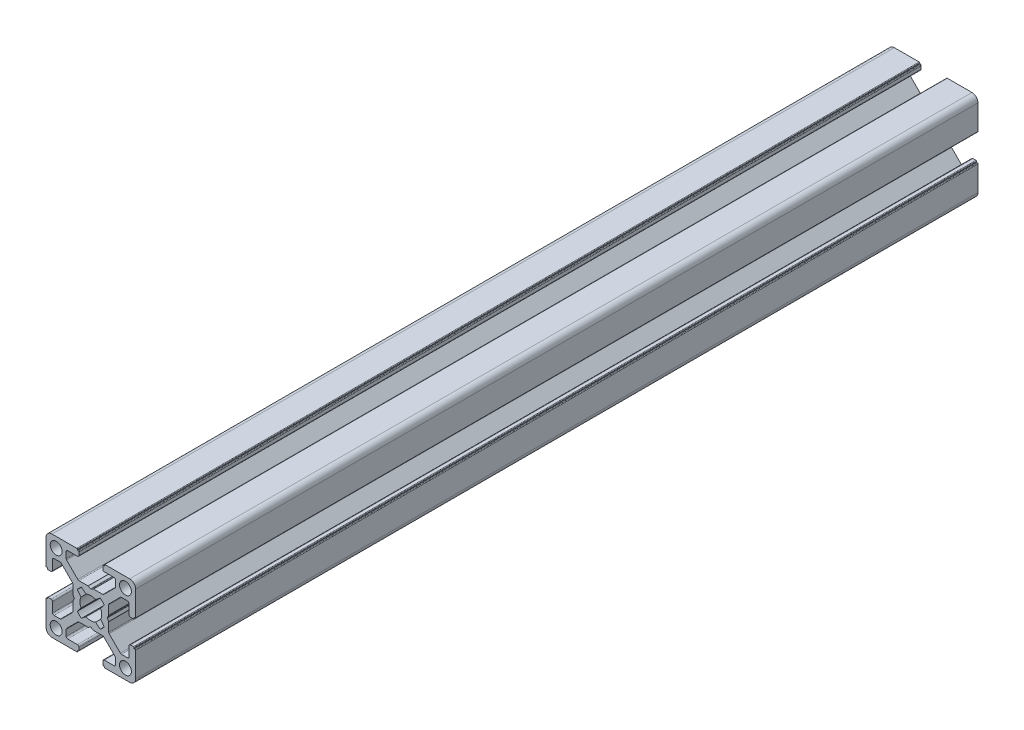
SolidWorks part; units mm, degrees
ref_plane "Alzado" through (0, 0, 0) normal (0, 0, 1) x (1, 0, 0)
ref_plane "Planta" through (0, 0, 0) normal (0, 1, 0) x (1, 0, 0)
ref_plane "Vista lateral" through (0, 0, 0) normal (1, 0, 0) x (0, 0, -1)
ref_plane "Plano1" through (0, 0, 1000) normal (0, 0, 1) x (1, 0, 0)
sketch "Croquis1" plane through (0, 0, 1000) normal (0, 0, 1) x (1, 0, 0)
  line L16 (-7.8359, -10.4816) -> (-6.3001, -11.7194)
  line L17 (-3.0999, -11.7194) -> (-1.5641, -10.4816)
  line L18 (-0.1947, -11.8453) -> (-1.4194, -13.3999)
  line L19 (-1.4194, -16.6001) -> (-0.1947, -18.1547)
  line L20 (-1.5641, -19.5184) -> (-3.0999, -18.2806)
  line L21 (-6.3001, -18.2806) -> (-7.8359, -19.5184)
  line L22 (-9.2053, -18.1547) -> (-7.9806, -16.6001)
  line L23 (-7.9806, -13.3999) -> (-9.2053, -11.8453)
  line L24 (9.8, -10.5) -> (10.1, -10.5)
  line L25 (10.3, -10.3) -> (10.3, -2)
  line L26 (8.3, 0) -> (0, 0)
  line L27 (-0.2, -0.2) -> (-0.2, -0.5)
  line L28 (-0.2, -0.5) -> (-0.5, -0.5)
  line L29 (-0.7, -0.7) -> (-0.7, -1.7)
  line L30 (-0.2, -2.2) -> (3.05, -2.2)
  line L31 (3.55, -2.7) -> (3.55, -4.7431)
  line L32 (3.4037, -5.0964) -> (-0.3491, -8.8534)
  line L33 (-0.7028, -9) -> (-3.7468, -9)
  line L34 (-3.8462, -9.0264) -> (-4.6006, -9.4583)
  line L35 (-4.7994, -9.4583) -> (-5.5538, -9.0264)
  line L36 (-5.6532, -9) -> (-8.6972, -9)
  line L37 (-9.0509, -8.8534) -> (-12.8037, -5.0964)
  line L38 (-12.95, -4.7431) -> (-12.95, -2.7)
  line L39 (-12.45, -2.2) -> (-9.2, -2.2)
  line L40 (-8.7, -1.7) -> (-8.7, -0.7)
  line L41 (-8.9, -0.5) -> (-9.2, -0.5)
  line L42 (-9.2, -0.5) -> (-9.2, -0.2)
  line L43 (-9.4, 0) -> (-17.7, 0)
  line L44 (-19.7, -2) -> (-19.7, -10.3)
  line L45 (-19.5, -10.5) -> (-19.2, -10.5)
  line L46 (-19.2, -10.5) -> (-19.2, -10.8)
  line L47 (-19, -11) -> (-18, -11)
  line L48 (-17.5, -10.5) -> (-17.5, -7.25)
  line L49 (-17, -6.75) -> (-14.9569, -6.75)
  line L50 (-14.6036, -6.8963) -> (-10.8466, -10.6491)
  line L51 (-10.7, -11.0028) -> (-10.7, -14.0468)
  line L52 (-10.6736, -14.1462) -> (-10.2417, -14.9006)
  line L53 (-10.2417, -15.0994) -> (-10.6736, -15.8538)
  line L54 (-10.7, -15.9532) -> (-10.7, -18.9972)
  line L55 (-10.8466, -19.3509) -> (-14.6036, -23.1037)
  line L56 (-14.9569, -23.25) -> (-17, -23.25)
  line L57 (-17.5, -22.75) -> (-17.5, -19.5)
  line L58 (-18, -19) -> (-19, -19)
  line L59 (-19.2, -19.2) -> (-19.2, -19.5)
  line L60 (-19.2, -19.5) -> (-19.5, -19.5)
  line L61 (-19.7, -19.7) -> (-19.7, -28)
  line L62 (-17.7, -30) -> (-9.4, -30)
  line L63 (-9.2, -29.8) -> (-9.2, -29.5)
  line L64 (-9.2, -29.5) -> (-8.9, -29.5)
  line L65 (-8.7, -29.3) -> (-8.7, -28.3)
  line L66 (-9.2, -27.8) -> (-12.45, -27.8)
  line L67 (-12.95, -27.3) -> (-12.95, -25.2569)
  line L68 (-12.8037, -24.9036) -> (-9.0509, -21.1466)
  line L69 (-8.6972, -21) -> (-5.6532, -21)
  line L70 (-5.5538, -20.9736) -> (-4.7994, -20.5417)
  line L71 (-4.6006, -20.5417) -> (-3.8462, -20.9736)
  line L72 (-3.7468, -21) -> (-0.7028, -21)
  line L73 (-0.3491, -21.1466) -> (3.4037, -24.9036)
  line L74 (3.55, -25.2569) -> (3.55, -27.3)
  line L75 (3.05, -27.8) -> (-0.2, -27.8)
  line L76 (-0.7, -28.3) -> (-0.7, -29.3)
  line L77 (-0.5, -29.5) -> (-0.2, -29.5)
  line L78 (-0.2, -29.5) -> (-0.2, -29.8)
  line L79 (0, -30) -> (8.3, -30)
  line L80 (10.3, -28) -> (10.3, -19.7)
  line L81 (10.1, -19.5) -> (9.8, -19.5)
  line L82 (9.8, -19.5) -> (9.8, -19.2)
  line L83 (9.6, -19) -> (8.6, -19)
  line L84 (8.1, -19.5) -> (8.1, -22.75)
  line L85 (7.6, -23.25) -> (5.5569, -23.25)
  line L86 (5.2036, -23.1037) -> (1.4466, -19.3509)
  line L87 (1.3, -18.9972) -> (1.3, -15.9532)
  line L88 (1.2736, -15.8538) -> (0.8417, -15.0994)
  line L89 (0.8417, -14.9006) -> (1.2736, -14.1462)
  line L90 (1.3, -14.0468) -> (1.3, -11.0028)
  line L91 (1.4466, -10.6491) -> (5.2036, -6.8963)
  line L92 (5.5569, -6.75) -> (7.6, -6.75)
  line L93 (8.1, -7.25) -> (8.1, -10.5)
  line L94 (8.6, -11) -> (9.6, -11)
  line L95 (9.8, -10.8) -> (9.8, -10.5)
  line L96 (8, -2.3) -> (5.8, -4.5) construction
  line L97 (-15.2, -2.3) -> (-17.4, -4.5) construction
  line L98 (-4.7, -15) -> (6.9, -15) construction
  arc A16 (-9.2053, -11.8453) -> (-7.8359, -10.4816) centre (-4.7, -15) cw
  arc A17 (-6.3001, -11.7194) -> (-3.0999, -11.7194) centre (-4.7, -15) cw
  arc A18 (-1.5641, -10.4816) -> (-0.1947, -11.8453) centre (-4.7, -15) cw
  arc A19 (-1.4194, -13.3999) -> (-1.4194, -16.6001) centre (-4.7, -15) cw
  arc A20 (-0.1947, -18.1547) -> (-1.5641, -19.5184) centre (-4.7, -15) cw
  arc A21 (-3.0999, -18.2806) -> (-6.3001, -18.2806) centre (-4.7, -15) cw
  arc A22 (-7.8359, -19.5184) -> (-9.2053, -18.1547) centre (-4.7, -15) cw
  arc A23 (-7.9806, -16.6001) -> (-7.9806, -13.3999) centre (-4.7, -15) cw
  arc A24 (10.1, -10.5) -> (10.3, -10.3) centre (10.1, -10.3) ccw
  arc A25 (10.3, -2) -> (8.3, 0) centre (8.3, -2) ccw
  arc A26 (0, 0) -> (-0.2, -0.2) centre (0, -0.2) ccw
  arc A27 (-0.5, -0.5) -> (-0.7, -0.7) centre (-0.5, -0.7) ccw
  arc A28 (-0.7, -1.7) -> (-0.2, -2.2) centre (-0.2, -1.7) ccw
  arc A29 (3.05, -2.2) -> (3.55, -2.7) centre (3.05, -2.7) cw
  arc A30 (3.55, -4.7431) -> (3.4037, -5.0964) centre (3.05, -4.7431) cw
  arc A31 (-0.3491, -8.8534) -> (-0.7028, -9) centre (-0.7028, -8.5) cw
  arc A32 (-3.7468, -9) -> (-3.8462, -9.0264) centre (-3.7468, -9.2) ccw
  arc A33 (-4.6006, -9.4583) -> (-4.7994, -9.4583) centre (-4.7, -9.2847) cw
  arc A34 (-5.5538, -9.0264) -> (-5.6532, -9) centre (-5.6532, -9.2) ccw
  arc A35 (-8.6972, -9) -> (-9.0509, -8.8534) centre (-8.6972, -8.5) cw
  arc A36 (-12.8037, -5.0964) -> (-12.95, -4.7431) centre (-12.45, -4.7431) cw
  arc A37 (-12.95, -2.7) -> (-12.45, -2.2) centre (-12.45, -2.7) cw
  arc A38 (-9.2, -2.2) -> (-8.7, -1.7) centre (-9.2, -1.7) ccw
  arc A39 (-8.7, -0.7) -> (-8.9, -0.5) centre (-8.9, -0.7) ccw
  arc A40 (-9.2, -0.2) -> (-9.4, 0) centre (-9.4, -0.2) ccw
  arc A41 (-17.7, 0) -> (-19.7, -2) centre (-17.7, -2) ccw
  arc A42 (-19.7, -10.3) -> (-19.5, -10.5) centre (-19.5, -10.3) ccw
  arc A43 (-19.2, -10.8) -> (-19, -11) centre (-19, -10.8) ccw
  arc A44 (-18, -11) -> (-17.5, -10.5) centre (-18, -10.5) ccw
  arc A45 (-17.5, -7.25) -> (-17, -6.75) centre (-17, -7.25) cw
  arc A46 (-14.9569, -6.75) -> (-14.6036, -6.8963) centre (-14.9569, -7.25) cw
  arc A47 (-10.8466, -10.6491) -> (-10.7, -11.0028) centre (-11.2, -11.0028) cw
  arc A48 (-10.7, -14.0468) -> (-10.6736, -14.1462) centre (-10.5, -14.0468) ccw
  arc A49 (-10.2417, -14.9006) -> (-10.2417, -15.0994) centre (-10.4153, -15) cw
  arc A50 (-10.6736, -15.8538) -> (-10.7, -15.9532) centre (-10.5, -15.9532) ccw
  arc A51 (-10.7, -18.9972) -> (-10.8466, -19.3509) centre (-11.2, -18.9972) cw
  arc A52 (-14.6036, -23.1037) -> (-14.9569, -23.25) centre (-14.9569, -22.75) cw
  arc A53 (-17, -23.25) -> (-17.5, -22.75) centre (-17, -22.75) cw
  arc A54 (-17.5, -19.5) -> (-18, -19) centre (-18, -19.5) ccw
  arc A55 (-19, -19) -> (-19.2, -19.2) centre (-19, -19.2) ccw
  arc A56 (-19.5, -19.5) -> (-19.7, -19.7) centre (-19.5, -19.7) ccw
  arc A57 (-19.7, -28) -> (-17.7, -30) centre (-17.7, -28) ccw
  arc A58 (-9.4, -30) -> (-9.2, -29.8) centre (-9.4, -29.8) ccw
  arc A59 (-8.9, -29.5) -> (-8.7, -29.3) centre (-8.9, -29.3) ccw
  arc A60 (-8.7, -28.3) -> (-9.2, -27.8) centre (-9.2, -28.3) ccw
  arc A61 (-12.45, -27.8) -> (-12.95, -27.3) centre (-12.45, -27.3) cw
  arc A62 (-12.95, -25.2569) -> (-12.8037, -24.9036) centre (-12.45, -25.2569) cw
  arc A63 (-9.0509, -21.1466) -> (-8.6972, -21) centre (-8.6972, -21.5) cw
  arc A64 (-5.6532, -21) -> (-5.5538, -20.9736) centre (-5.6532, -20.8) ccw
  arc A65 (-4.7994, -20.5417) -> (-4.6006, -20.5417) centre (-4.7, -20.7153) cw
  arc A66 (-3.8462, -20.9736) -> (-3.7468, -21) centre (-3.7468, -20.8) ccw
  arc A67 (-0.7028, -21) -> (-0.3491, -21.1466) centre (-0.7028, -21.5) cw
  arc A68 (3.4037, -24.9036) -> (3.55, -25.2569) centre (3.05, -25.2569) cw
  arc A69 (3.55, -27.3) -> (3.05, -27.8) centre (3.05, -27.3) cw
  arc A70 (-0.2, -27.8) -> (-0.7, -28.3) centre (-0.2, -28.3) ccw
  arc A71 (-0.7, -29.3) -> (-0.5, -29.5) centre (-0.5, -29.3) ccw
  arc A72 (-0.2, -29.8) -> (0, -30) centre (0, -29.8) ccw
  arc A73 (8.3, -30) -> (10.3, -28) centre (8.3, -28) ccw
  arc A74 (10.3, -19.7) -> (10.1, -19.5) centre (10.1, -19.7) ccw
  arc A75 (9.8, -19.2) -> (9.6, -19) centre (9.6, -19.2) ccw
  arc A76 (8.6, -19) -> (8.1, -19.5) centre (8.6, -19.5) ccw
  arc A77 (8.1, -22.75) -> (7.6, -23.25) centre (7.6, -22.75) cw
  arc A78 (5.5569, -23.25) -> (5.2036, -23.1037) centre (5.5569, -22.75) cw
  arc A79 (1.4466, -19.3509) -> (1.3, -18.9972) centre (1.8, -18.9972) cw
  arc A80 (1.3, -15.9532) -> (1.2736, -15.8538) centre (1.1, -15.9532) ccw
  arc A81 (0.8417, -15.0994) -> (0.8417, -14.9006) centre (1.0153, -15) cw
  arc A82 (1.2736, -14.1462) -> (1.3, -14.0468) centre (1.1, -14.0468) ccw
  arc A83 (1.3, -11.0028) -> (1.4466, -10.6491) centre (1.8, -11.0028) cw
  arc A84 (5.2036, -6.8963) -> (5.5569, -6.75) centre (5.5569, -7.25) cw
  arc A85 (7.6, -6.75) -> (8.1, -7.25) centre (7.6, -7.25) cw
  arc A86 (8.1, -10.5) -> (8.6, -11) centre (8.6, -10.5) ccw
  arc A87 (9.6, -11) -> (9.8, -10.8) centre (9.6, -10.8) ccw
  circle A88 centre (-16.3, -3.4) radius 2
  circle A89 centre (6.9, -3.4) radius 2
  circle A90 centre (-16.3, -26.6) radius 2
  circle A91 centre (6.9, -26.6) radius 2
  dimension "D3" = 4
  dimension "D1" = 30
  dimension "D2" = 30
  dimension "D4" = 23.2
  dimension "D5" = 23.2
extrude "Saliente-Extruir1" add sketch "Croquis1" against normal blind 282
